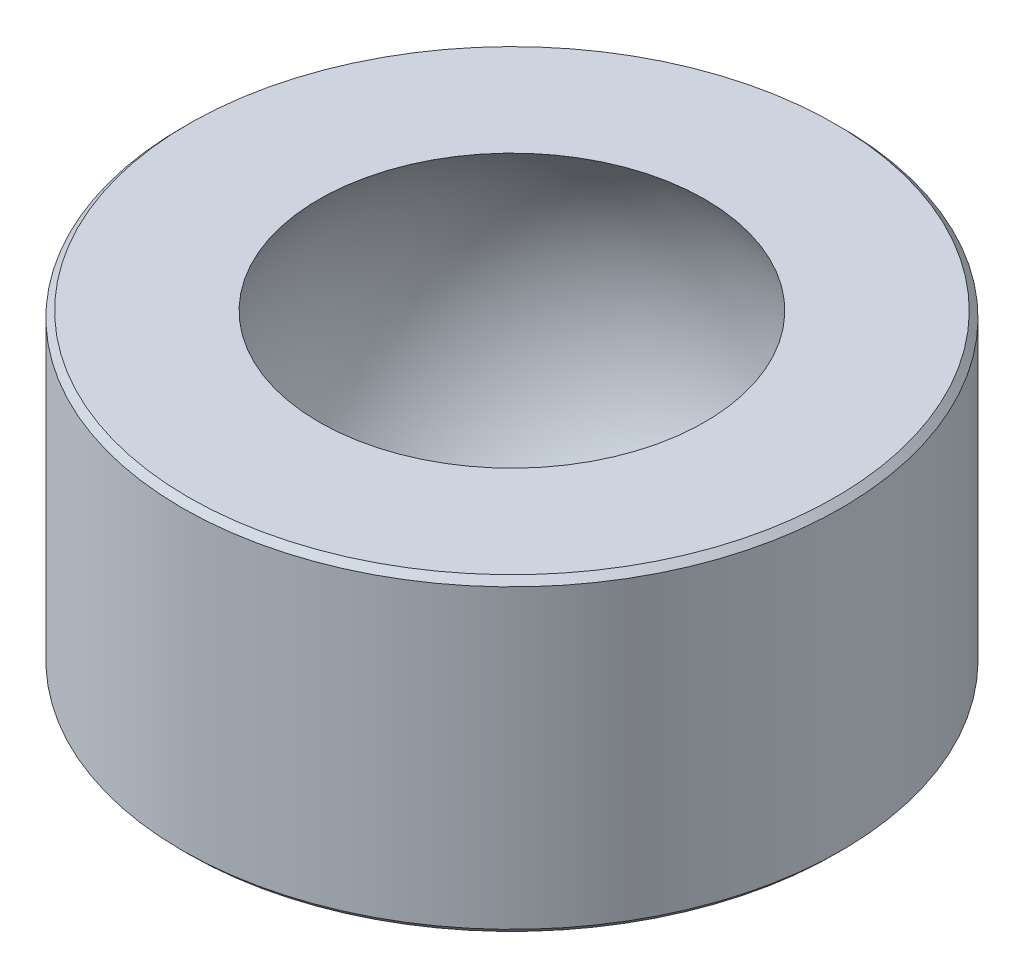
SolidWorks part; units mm, degrees
material "Aleación 1060"
ref_plane "Front Plane" through (0, 0, 0) normal (0, 0, 1) x (1, 0, 0)
ref_plane "Top Plane" through (0, 0, 0) normal (0, 1, 0) x (1, 0, 0)
ref_plane "Right Plane" through (0, 0, 0) normal (1, 0, 0) x (0, 0, -1)
sketch "Sketch1" plane through (0, 0, 0) normal (0, 1, 0) x (1, 0, 0)
  circle A0 centre (0, 0) radius 2
  circle A1 centre (0, 0) radius 3 construction
  circle A2 centre (0, 0) radius 4
  dimension "D1" = 8
  dimension "D2" = 6
  dimension "D3" = 4
extrude "Boss-Extrude1" add sketch "Sketch1" along normal mid plane 3.75
sketch "Sketch2" plane through (0, 0, 0) normal (0, 1, 0) x (1, 0, 0)
  line L0 (0, 3) -> (0, -3)
  circle A0 centre (0, 0) radius 3 construction
  arc A1 (0, 3) -> (0, -3) centre (0, 0) ccw
revolve "Revolve1" add sketch "Sketch2" angle 360 about L0
combine bodies "Combine1" operation type subtract main body 101 bodies to subtract 102
chamfer "Chamfer1" distance 0.075 angle 45 2 edges at (0, -1.875, 4) (0, 1.875, 4)
